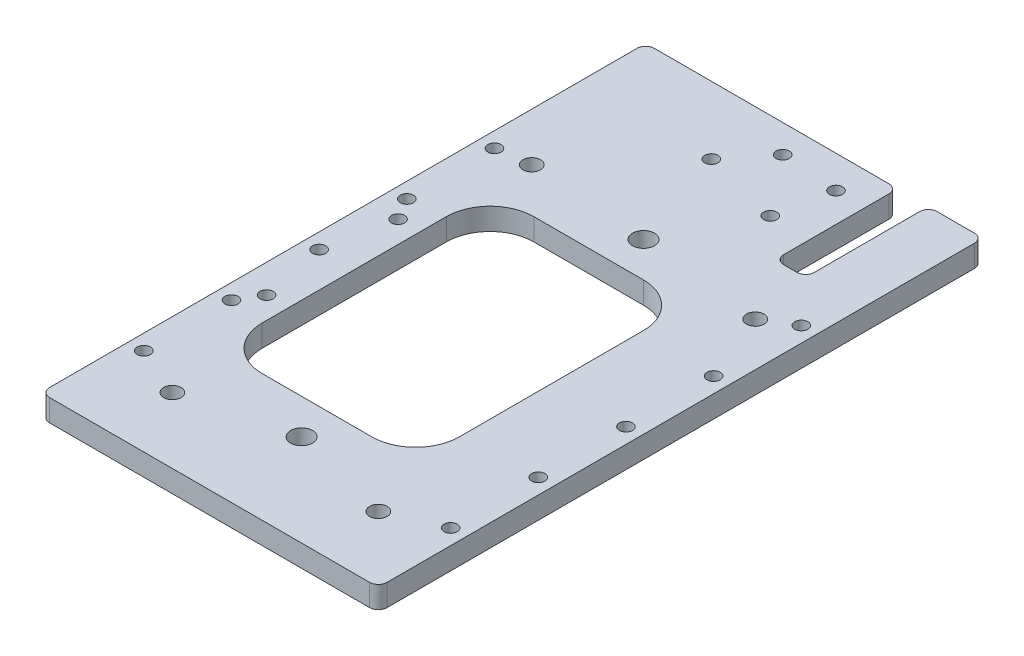
SolidWorks part; units mm, degrees
ref_plane "前视基准面" through (0, 0, 0) normal (0, 0, 1) x (1, 0, 0)
ref_plane "上视基准面" through (0, 0, 0) normal (0, 1, 0) x (1, 0, 0)
ref_plane "右视基准面" through (0, 0, 0) normal (1, 0, 0) x (0, 0, -1)
sketch "草图1" plane through (0, 0, 0) normal (0, 1, 0) x (1, 0, 0)
  line L0 (38.5, -77) -> (38.5, 77) construction
  line L1 (-38.5, 78) -> (38.5, 78)
  line L2 (-38.5, 78) -> (-38.5, -60)
  line L3 (-38.5, -60) -> (38.5, -60)
  line L4 (38.5, 78) -> (38.5, -60)
  line L5 (0, -60) -> (0, 78) construction
  line L6 (-38.5, 0) -> (38.5, 0) construction
  line L8 (18, 31) -> (-27, 31)
  line L9 (18, 31) -> (18, -31)
  line L10 (18, -31) -> (-27, -31)
  line L11 (-27, 31) -> (-27, -31)
  line L13 (18, 0) -> (-27, 0) construction
  circle A0 centre (0, 39) radius 2.5
  circle A1 centre (0, -39) radius 2.5
  point P1 (0, 0)
  point P7 (0, 0)
  dimension "D2" = 18
  dimension "D6" = 5
  dimension "D1" = 138
  dimension "D3" = 62
  dimension "D4" = 27
  dimension "D5" = 60
  dimension "D7" = 78
extrude "凸台-拉伸1" add sketch "草图1" along normal blind 5
sketch "草图7" plane through (0, 5, 0) normal (0, 1, 0) x (1, 0, 0)
  line L0 (38.5, 78) -> (-38.5, 78) construction
  line L1 (19, 78) -> (26, 78)
  line L2 (19, 78) -> (19, 50)
  line L3 (19, 50) -> (26, 50)
  line L4 (26, 78) -> (26, 50)
  line L8 (38.5, -60) -> (38.5, 78) construction
  dimension "D1" = 28
  dimension "D2" = 7
  dimension "D3" = 12.5
extrude "切除-拉伸1" cut sketch "草图7" against normal through all
hole_wizard "大小mm Clearance 暗销孔0" positions "草图5" profile "草图6" hole size "Ø4.0" standard "GB" end condition through all
sketch "草图5" plane through (0, 0, 0) normal (0, -1, 0) x (-1, 0, 0)
  line L6 (38.5, 78) -> (38.5, -60) construction
  line L8 (0, -66.1303) -> (0, 98.0111) construction
  line L10 (-38.5, -60) -> (-38.5, 78) construction
  line L11 (38.5, -60) -> (-38.5, -60) construction
  line L12 (-18, 31) -> (27, 31) construction
  point P0 (-28.5, 36)
  point P19 (27.5, 41)
  point P24 (23.5, -45)
  point P26 (-23.5, -45)
  dimension "D1" = 15
  dimension "D2" = 15
  dimension "D3" = 11
  dimension "D4" = 5
  dimension "D5" = 10
  dimension "D6" = 10
sketch "草图6" plane through (28.5, 0, -36) normal (1, 0, 0) x (0, 0, -1)
  line L0 (0, 0) -> (0, 5)
  line L1 (0, 5) -> (2, 5)
  line L2 (2, 5) -> (2, 0)
  line L5 (2, 0) -> (0, 0)
  line L11 (0, -6.35) -> (0, 107.95) construction
  dimension "通孔孔直径" = 4
  dimension "通孔孔深度" = 5
fillet "圆角1" radius 10 4 edges at (18, 2.5, -31) (18, 2.5, 31) (-27, 2.5, 31) (-27, 2.5, -31)
fillet "圆角2" radius 2 8 edges at (38.5, 2.5, 60) (-38.5, 2.5, 60) (-38.5, 2.5, -78) (38.5, 2.5, -78) (19, 2.5, -78) (26, 2.5, -78) (19, 2.5, -50) (26, 2.5, -50)
hole_wizard "大小mm Transitional 暗销孔0" positions "草图8" profile "草图9" hole size "Ø3.0" standard "GB" end condition through all
sketch "草图8" plane through (0, 5, 0) normal (0, 1, 0) x (1, 0, 0)
  line L0 (-42.0949, 0) -> (25.7956, 0) construction
  line L1 (0, -15) -> (0, 81.2598) construction
  point P0 (-32, 15)
  point P3 (-32, -15)
  point P16 (-8.1429, 62.6128)
  point P19 (-0.8571, 71.6128)
  point P22 (12.3094, 70.6128)
  point P25 (9.8094, 58.1128)
  dimension "D10" = 0.8571
  dimension "D1" = 15
  dimension "D2" = 32
  dimension "D3" = 62.6128
  dimension "D4" = 8.1429
  dimension "D5" = 9
  dimension "D6" = 9.8094
  dimension "D7" = 12.5
  dimension "D8" = 12.3094
  dimension "D9" = 58.1128
sketch "草图9" plane through (-32, 5, -15) normal (1, 0, 0) x (0, 0, 1)
  line L0 (0, 0) -> (0, 5)
  line L1 (0, 5) -> (1.5, 5)
  line L2 (1.5, 5) -> (1.5, 0)
  line L5 (1.5, 0) -> (0, 0)
  line L11 (0, -6.35) -> (0, 107.95) construction
  dimension "通孔孔直径" = 3
  dimension "通孔孔深度" = 5
hole_wizard "大小mm Clearance 暗销孔0" positions "草图12" profile "草图11" hole size "Ø3.0" standard "GB"
sketch "草图12" plane through (0, 5, 0) normal (0, 1, 0) x (1, 0, 0)
  line L0 (41.7758, 0) -> (-45.906, 0) construction
  line L2 (-38.5, 76) -> (-38.5, -58) construction
  line L4 (0, -18.1554) -> (0, 17.8991) construction
  point P0 (-35, 0)
  point P53 (35, 50) [skipped]
  point P54 (35, 25) [skipped]
  point P67 (-35, 20)
  point P68 (-35, 40)
  point P73 (-35, -40)
  point P74 (-35, -20)
  point P75 (35, 40)
  point P76 (35, 20)
  point P77 (35, 0)
  point P78 (35, -20)
  point P79 (35, -40)
  dimension "D1" = 3.5
  dimension "D2" = 3
sketch "草图11" plane through (-35, 5, 0) normal (1, 0, 0) x (0, 0, 1)
  line L0 (0, 0) -> (0, 5)
  line L1 (0, 5) -> (1.5, 5)
  line L2 (1.5, 5) -> (1.5, 0)
  line L5 (1.5, 0) -> (0, 0)
  line L11 (0, -6.35) -> (0, 107.95) construction
  dimension "通孔孔直径" = 3
  dimension "通孔孔深度" = 5
